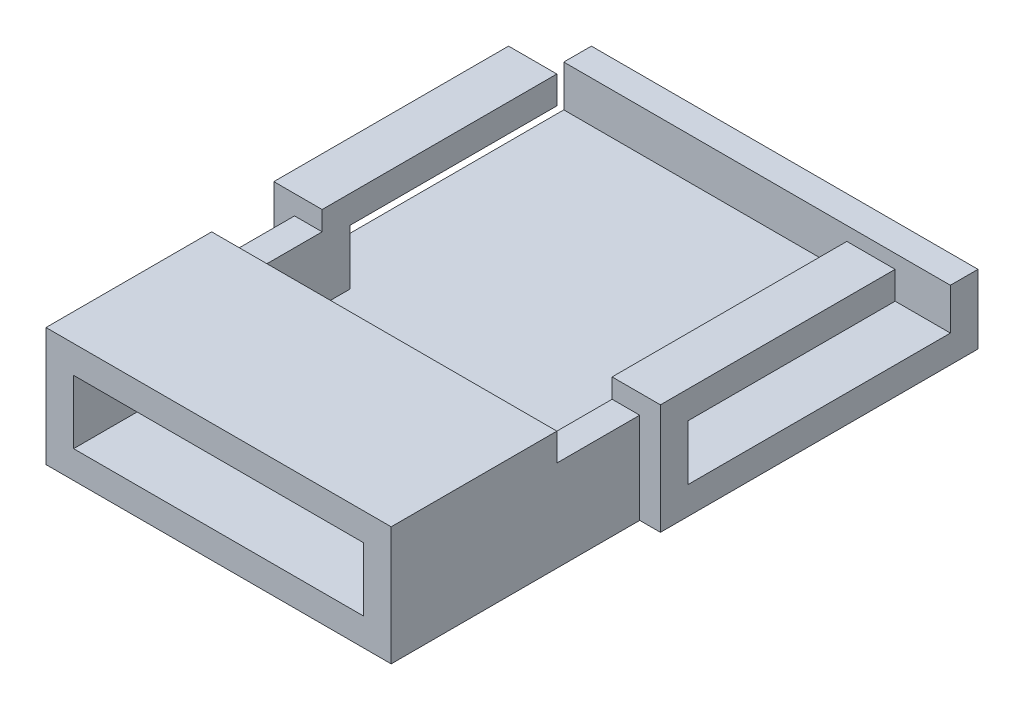
SolidWorks part; units mm, degrees
ref_plane "前视基准面" through (0, 0, 0) normal (0, 0, 1) x (1, 0, 0)
ref_plane "上视基准面" through (0, 0, 0) normal (0, 1, 0) x (1, 0, 0)
ref_plane "右视基准面" through (0, 0, 0) normal (1, 0, 0) x (0, 0, -1)
other "Configuration Table"
sketch "草图1" plane through (0, 0, 0) normal (0, 1, 0) x (1, 0, 0)
  line L0 (-5.25, -4) -> (5.25, -4)
  line L1 (0, 0) -> (6, 0)
  line L2 (0, 0) -> (0, 9.5)
  line L3 (0, 9.5) -> (6, 9.5)
  line L4 (6, 0) -> (6, 9.5)
  line L5 (0, 0) -> (-6, 0)
  line L6 (0, 0) -> (0, 9.5)
  line L7 (0, 9.5) -> (-6, 9.5)
  line L8 (-6, 0) -> (-6, 9.5)
  line L9 (-5.25, 0) -> (5.25, 0)
  line L10 (-5.25, 0) -> (-5.25, -9)
  line L11 (-5.25, -9) -> (5.25, -9)
  line L12 (5.25, 0) -> (5.25, -9)
  dimension "D1" = 9.5
  dimension "D2" = 10.5
  dimension "D3" = 5.25
  dimension "D4" = 6
  dimension "D5" = 6
  dimension "D6" = 9
  dimension "D7" = 5
sketch "草图2" plane through (0, 0, 0) normal (0, 1, 0) x (1, 0, 0)
  line L1 (-6, 9.5) -> (6, 9.5)
  line L2 (-6, 9.5) -> (-6, 0)
  line L3 (-6, 0) -> (6, 0)
  line L4 (6, 9.5) -> (6, 0)
  line L5 (5.25, -9) -> (-5.25, -9)
  line L6 (5.25, -9) -> (5.25, 0)
  line L7 (5.25, 0) -> (-5.25, 0)
  line L8 (-5.25, -9) -> (-5.25, 0)
extrude "凸台-拉伸1" add sketch "草图2" along normal blind 1 contours L4 L1 L2 L3 | L8 L5 L6 L3
sketch "草图3" plane through (0, 1, 0) normal (0, 1, 0) x (1, 0, 0)
  line L0 (7, -1) -> (7, 10.5)
  line L1 (7, 10.5) -> (-7, 10.5)
  line L2 (-7, 10.5) -> (-7, -1)
  line L3 (-7, -1) -> (-6.25, -1)
  line L4 (-6.25, -1) -> (-6.25, -10)
  line L5 (-6.25, -10) -> (6.25, -10)
  line L6 (6.25, -10) -> (6.25, -1)
  line L7 (6.25, -1) -> (7, -1)
  line L8 (6, 0) -> (6, 9.5)
  line L9 (6, 9.5) -> (-6, 9.5)
  line L10 (-6, 9.5) -> (-6, 0)
  line L11 (-6, 0) -> (-5.25, 0)
  line L12 (-5.25, 0) -> (-5.25, -9)
  line L13 (-5.25, -9) -> (5.25, -9)
  line L14 (5.25, -9) -> (5.25, 0)
  line L15 (5.25, 0) -> (6, 0)
  line L16 (6, 0) -> (6, 9.5)
  line L17 (6, 9.5) -> (-6, 9.5)
  line L18 (-6, 9.5) -> (-6, 0)
  line L19 (-6, 0) -> (-5.25, 0)
  line L20 (-5.25, 0) -> (-5.25, -9)
  line L21 (-5.25, -9) -> (5.25, -9)
  line L22 (5.25, -9) -> (5.25, 0)
  line L23 (5.25, 0) -> (6, 0)
  dimension "D1" = 0
  dimension "D2" = 1
extrude "凸台-拉伸2" add sketch "草图3" along normal blind 2.3 and the other way blind 1
sketch "草图4" plane through (0, 3.3, 0) normal (0, 1, 0) x (1, 0, 0)
  line L0 (-7, 10.5) -> (-7, -1) construction
  line L1 (-6, 0) -> (-7, 0)
  line L2 (-6, 0) -> (-6, 9.5)
  line L3 (-6, 9.5) -> (-7, 9.5)
  line L4 (-7, 0) -> (-7, 9.5)
  line L5 (7, -1) -> (7, 10.5) construction
  line L6 (6, 9.5) -> (7, 9.5)
  line L7 (6, 9.5) -> (6, 0)
  line L8 (6, 0) -> (7, 0)
  line L9 (7, 9.5) -> (7, 0)
  line L10 (-6.25, -10) -> (6.25, -10) construction
  line L11 (-5.25, -9) -> (5.25, -9)
  line L12 (-5.25, -9) -> (-5.25, -10)
  line L13 (-5.25, -10) -> (5.25, -10)
  line L14 (5.25, -9) -> (5.25, -10)
  line L15 (5.25, 0) -> (5.25, -9) construction
  line L16 (0, 9.5) -> (-6, 9.5) construction
  line L17 (0, 0) -> (6, 0) construction
extrude "切除-拉伸1" cut sketch "草图4" against normal blind 2.3
sketch "草图5" plane through (0, 3.3, 0) normal (0, 1, 0) x (1, 0, 0)
  line L0 (6.25, -10) -> (6.25, -1) construction
  line L1 (-6.25, -10) -> (6.25, -10)
  line L2 (-6.25, -10) -> (-6.25, -4)
  line L3 (-6.25, -4) -> (6.25, -4)
  line L4 (6.25, -10) -> (6.25, -4)
  line L5 (-5.25, -4) -> (5.25, -4) construction
extrude "凸台-拉伸3" add sketch "草图5" along normal blind 1
sketch "草图6" plane through (0, 3.3, 0) normal (0, 1, 0) x (1, 0, 0)
  line L0 (-5.25, 0) -> (-5.25, -9) construction
  line L1 (-7, 0) -> (-5.25, 0)
  line L2 (-7, 0) -> (-7, -1)
  line L3 (-7, -1) -> (-5.25, -1)
  line L4 (-5.25, 0) -> (-5.25, -1)
  line L5 (5.25, 0) -> (5.25, -9) construction
  line L6 (7, 0) -> (5.25, 0)
  line L7 (7, 0) -> (7, -1)
  line L8 (7, -1) -> (5.25, -1)
  line L9 (5.25, 0) -> (5.25, -1)
  line L10 (6.25, -1) -> (7, -1) construction
sketch "草图9" plane through (0, 3.3, 0) normal (0, 1, 0) x (1, 0, 0)
  line L4 (-7, 10.5) -> (-7, 9.5)
  line L5 (-7, 9.5) -> (7, 9.5)
  line L6 (7, 9.5) -> (7, 10.5)
  line L7 (7, 10.5) -> (-7, 10.5)
  line L8 (-7, 10.5) -> (-7, 9.5)
  line L9 (-7, 9.5) -> (7, 9.5)
  line L10 (7, 9.5) -> (7, 10.5)
  line L11 (7, 10.5) -> (-7, 10.5)
  dimension "D1" = 0
extrude "切除-拉伸3" cut sketch "草图6" against normal blind 0.3
extrude "切除-拉伸4" cut sketch "草图9" against normal blind 0.8
sketch "草图10" plane through (0, 3, 0) normal (0, 1, 0) x (1, 0, 0)
  line L0 (7, 10.5) -> (-7, 10.5) construction
  line L1 (-7, -1) -> (-5.25, -1)
  line L2 (-7, -1) -> (-7, 10.5)
  line L3 (-7, 10.5) -> (-5.25, 10.5)
  line L4 (-5.25, -1) -> (-5.25, 10.5)
  line L5 (-5.25, 0) -> (-5.25, -9) construction
  line L6 (7, -1) -> (5.25, -1)
  line L7 (7, -1) -> (7, 10.5)
  line L8 (7, 10.5) -> (5.25, 10.5)
  line L9 (5.25, -1) -> (5.25, 10.5)
  line L10 (5.25, 0) -> (5.25, -9) construction
  line L12 (-7, 10.5) -> (-5.25, 10.5)
  line L13 (-7, 10.5) -> (-7, 7.5)
  line L14 (-7, 7.5) -> (-5.25, 7.5)
  line L15 (-5.25, 10.5) -> (-5.25, 7.5)
  line L16 (5.25, 10.5) -> (7, 10.5)
  line L17 (5.25, 10.5) -> (5.25, 7.5)
  line L18 (5.25, 7.5) -> (7, 7.5)
  line L19 (7, 10.5) -> (7, 7.5)
  line L20 (-7, 9.5) -> (7, 9.5) construction
  line L21 (0, 9.5) -> (-6, 9.5) construction
  line M11 (-7, 0) -> (-7, -1)
  line M12 (-7, -1) -> (-6.25, -1)
  line M13 (-6.25, -1) -> (-5.25, -1)
  line M14 (-5.25, -1) -> (-5.25, 0)
  line M15 (-5.25, 0) -> (-7, 0)
  dimension "D1" = 2
  dimension "D2" = 2
extrude "凸台-拉伸7" add sketch "草图10" along normal blind 1 contours L14 L2 L4 M15 | L18 L9 L6 L7 | M15 M11 M12 M13 M14
